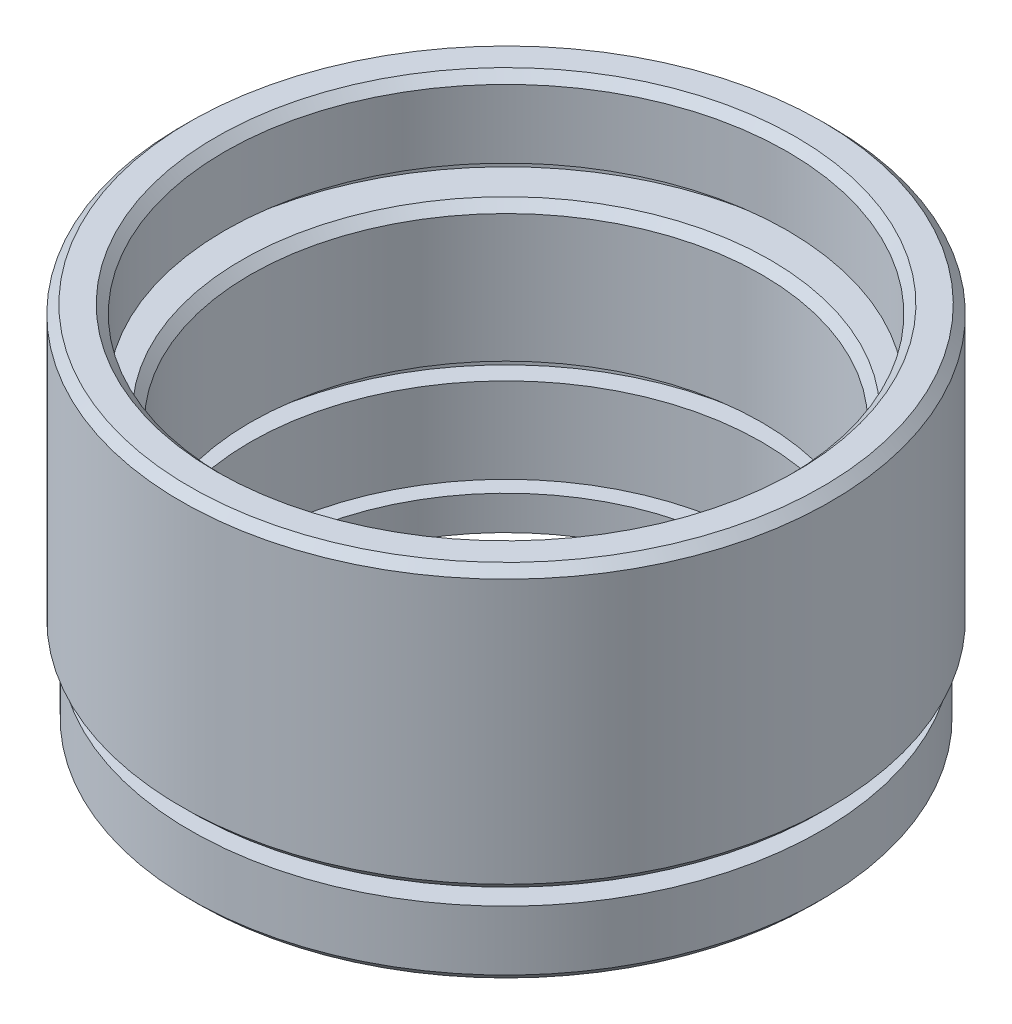
SolidWorks part; units mm, degrees
ref_plane "前视基准面" through (0, 0, 0) normal (0, 0, 1) x (1, 0, 0)
ref_plane "上视基准面" through (0, 0, 0) normal (0, 1, 0) x (1, 0, 0)
ref_plane "右视基准面" through (0, 0, 0) normal (1, 0, 0) x (0, 0, -1)
sketch "草图1" plane through (0, 0, 0) normal (0, 0, 1) x (1, 0, 0)
  line L0 (0, 0) -> (0, 51.3875) construction
  line L1 (14, 0) -> (14, 2)
  line L2 (14, 2) -> (15, 2)
  line L3 (15, 2) -> (15, 7)
  line L4 (15, 7) -> (16.15, 7)
  line L5 (16.15, 7) -> (16.15, 8)
  line L6 (16.15, 8) -> (15, 8)
  line L7 (15, 8) -> (15, 16)
  line L8 (15, 16) -> (17.65, 16)
  line L9 (14, 0) -> (18, 0)
  line L10 (17.65, 16) -> (17.65, 17)
  line L11 (17.65, 17) -> (16.5, 17)
  line L12 (16.5, 17) -> (16.5, 21.5)
  line L13 (16.5, 21.5) -> (18.55, 21.5)
  line L14 (0, 0) -> (5.8539, 0) construction
  line L15 (18.5, 0.5) -> (18.5, 4)
  line L16 (18.5, 4) -> (17, 4)
  line L17 (17, 4) -> (17, 5)
  line L18 (17, 5) -> (18.55, 5)
  line L19 (19.05, 5.5) -> (19.05, 21)
  line L20 (18, 0) -> (18.5, 0.5)
  line L21 (18.55, 5) -> (19.05, 5.5)
  line L22 (19.05, 21) -> (18.55, 21.5)
  point P13 (18.5, 0)
  point P22 (19.05, 5)
  point P24 (19.05, 21.5)
  dimension "D1" = 14
  dimension "D2" = 2
  dimension "D3" = 15
  dimension "D4" = 5
  dimension "D5" = 16.15
  dimension "D6" = 1
  dimension "D7" = 15
  dimension "D8" = 1
  dimension "D9" = 17.65
  dimension "D10" = 5.5
  dimension "D11" = 16.5
  dimension "D12" = 16.5
  dimension "D13" = 18.5
  dimension "D14" = 1
  dimension "D15" = 0.5
  dimension "D16" = 17
  dimension "D17" = 19.05
  dimension "D18" = 0.5
  dimension "D19" = 45
  dimension "D20" = 45
  dimension "D21" = 0.5
  dimension "D22" = 45
  dimension "D23" = 5
revolve "旋转1" add sketch "草图1" angle 360 about L0
cosmetic thread "装饰螺纹线1"
cosmetic thread "装饰螺纹线2"
cosmetic thread "装饰螺纹线3"
chamfer "倒角1" distance 0.5 angle 45 2 edges at (0, 16, -15) (0, 21.5, -16.5)
